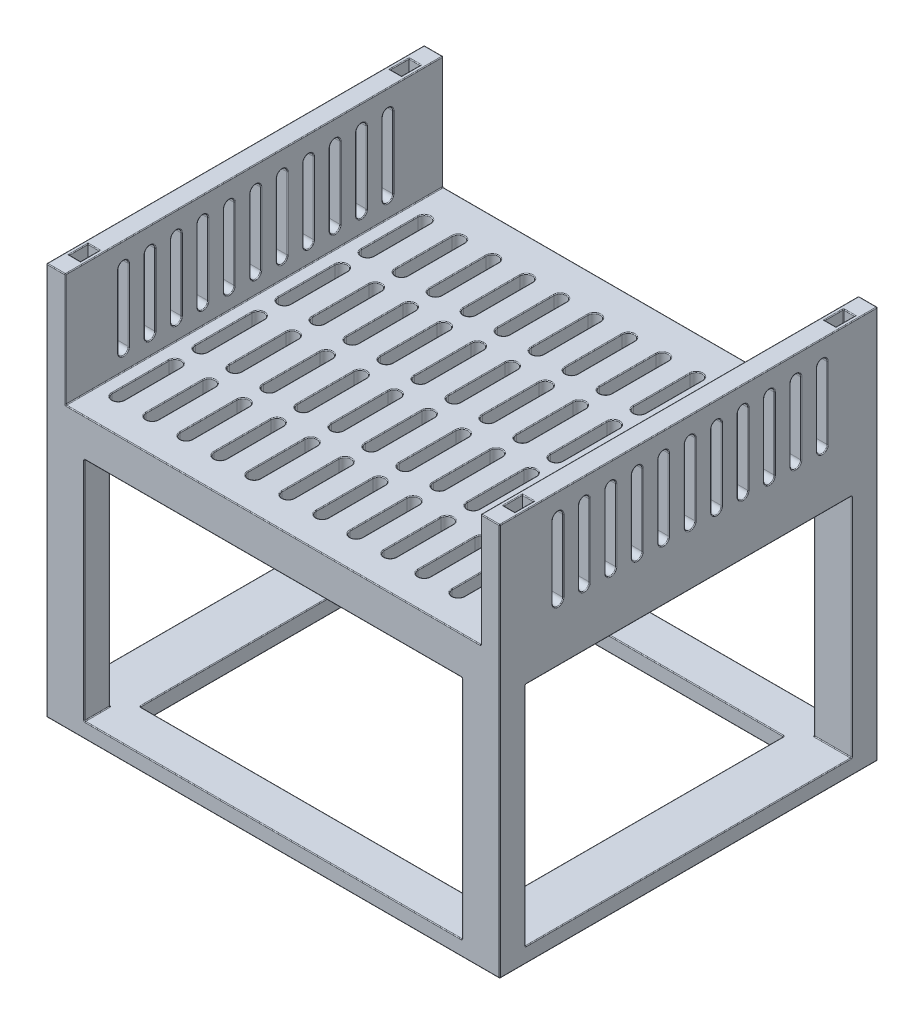
SolidWorks part; units mm, degrees
ref_plane "Plano frontal" through (0, 0, 0) normal (0, 0, 1) x (1, 0, 0)
ref_plane "Plano superior" through (0, 0, 0) normal (0, 1, 0) x (1, 0, 0)
ref_plane "Plano direito" through (0, 0, 0) normal (1, 0, 0) x (0, 0, -1)
sketch "Esboço1" plane through (0, 0, 0) normal (0, 1, 0) x (1, 0, 0)
  line L1 (0, 0) -> (600, 0)
  line L2 (0, 0) -> (0, 500)
  line L3 (0, 500) -> (600, 500)
  line L4 (600, 0) -> (600, 500)
  dimension "D1" = 500
  dimension "D2" = 600
extrude "Ressalto-extrusão1" add sketch "Esboço1" along normal blind 50
sketch "Esboço3" plane through (0, 50, 0) normal (0, 1, 0) x (1, 0, 0)
  line L0 (0, 0) -> (600, 0) construction
  line L1 (0, 500) -> (25, 500)
  line L2 (0, 500) -> (0, 0)
  line L3 (0, 0) -> (25, 0)
  line L4 (25, 500) -> (25, 0)
  line L6 (600, 500) -> (575, 500)
  line L7 (600, 500) -> (600, 0)
  line L8 (600, 0) -> (575, 0)
  line L9 (575, 500) -> (575, 0)
  dimension "D1" = 25
  dimension "D2" = 25
extrude "Ressalto-extrusão2" add sketch "Esboço3" along normal blind 150
sketch "Esboço13" plane through (0, 0, 0) normal (0, -1, 0) x (1, 0, 0)
  line L0 (50, -45) -> (50, -120) construction
  line L1 (58, -45) -> (58, -120)
  line L2 (42, -45) -> (42, -120)
  line L3 (0, -500) -> (0, 0) construction
  line L4 (0, 0) -> (600, 0) construction
  arc A0 (58, -45) -> (42, -45) centre (50, -45) ccw
  arc A1 (42, -120) -> (58, -120) centre (50, -120) ccw
  point P2 (50, -82.5)
  dimension "D2" = 8
  dimension "D1" = 75
  dimension "D3" = 50
  dimension "D4" = 45
extrude "Corte-extrusão6" cut sketch "Esboço13" against normal through all
pattern_linear "Padrão linear1" count 12 spacing 45 along (1, 0, 0) count 4 spacing 110 along (0, 0, -1) of "Corte-extrusão6"
sketch "Esboço15" plane through (0, 0, 0) normal (0, -1, 0) x (1, 0, 0)
  line L0 (300, 0) -> (300, -500) construction
  line L1 (0, 0) -> (50, 0)
  line L2 (0, 0) -> (0, -34)
  line L3 (0, -34) -> (50, -34)
  line L4 (50, 0) -> (50, -34)
  line L5 (0, 0) -> (600, 0) construction
  line L7 (0, -250) -> (600, -250) construction
  line L8 (0, -500) -> (0, 0) construction
  line L9 (600, 0) -> (600, -500) construction
  line L10 (550, 0) -> (550, -34)
  line L11 (600, -34) -> (550, -34)
  line L12 (600, 0) -> (600, -34)
  line L13 (600, 0) -> (550, 0)
  line L14 (600, -500) -> (550, -500)
  line L15 (600, -500) -> (600, -466)
  line L16 (600, -466) -> (550, -466)
  line L17 (550, -500) -> (550, -466)
  line L18 (50, -500) -> (50, -466)
  line L19 (0, -466) -> (50, -466)
  line L20 (0, -500) -> (0, -466)
  line L21 (0, -500) -> (50, -500)
  dimension "D1" = 34
  dimension "D2" = 50
extrude "Ressalto-extrusão4" add sketch "Esboço15" along normal blind 300
sketch "Esboço16" plane through (0, -300, 0) normal (0, -1, 0) x (1, 0, 0)
  line L0 (0, 0) -> (0, -34) construction
  line L1 (530, -54) -> (70, -54)
  line L2 (600, -54) -> (600, 0)
  line L3 (600, 0) -> (0, 0)
  line L4 (0, -51.6587) -> (0, 0)
  line L5 (50, 0) -> (0, 0) construction
  line L6 (600, -500) -> (600, -466) construction
  line L11 (50, -34) -> (50, 0) construction
  line L12 (0, 0) -> (70, 0)
  line L13 (0, 0) -> (0, -500)
  line L14 (0, -500) -> (70, -500)
  line L15 (70, -54) -> (70, -446)
  line L17 (50, -466) -> (0, -466) construction
  line L18 (0, -500) -> (600, -500)
  line L19 (0, -500) -> (0, -546)
  line L20 (70, -446) -> (530, -446)
  line L21 (600, -500) -> (600, -546)
  line L24 (600, 0) -> (530, 0)
  line L25 (600, 0) -> (600, -500)
  line L26 (600, -500) -> (530, -500)
  line L28 (550, -34) -> (600, -34) construction
  line L29 (530, -54) -> (530, -446)
  line L30 (550, 0) -> (550, -34) construction
  point P0 (300, -18.1706)
  line M18 (0, 0) -> (0, -34)
  line M19 (0, -34) -> (50, -34)
  line M20 (50, -34) -> (50, 0)
  line M21 (50, 0) -> (0, 0)
  dimension "D1" = 20
  dimension "D4" = 20
  dimension "D6" = 20
  dimension "D8" = 20
extrude "Ressalto-extrusão6" add sketch "Esboço16" along normal blind 20 contours L25 L2 L3 L4 L13 L14 L18 L21 L1 L29 L20 L15 M18 M21 M20 M19 | M21 M18 M19 M20
sketch "Esboço17" plane through (0, 200, 0) normal (0, 1, 0) x (1, 0, 0)
  line L0 (300, 500) -> (300, 0) construction
  line L1 (5, 475) -> (20, 475)
  line L2 (5, 475) -> (5, 450)
  line L3 (5, 450) -> (20, 450)
  line L4 (20, 475) -> (20, 450)
  line L5 (575, 500) -> (25, 500) construction
  line L6 (25, 0) -> (575, 0) construction
  line L7 (0, 250) -> (600, 250) construction
  line L8 (0, 500) -> (0, 0) construction
  line L9 (600, 0) -> (600, 500) construction
  line L10 (25, 500) -> (0, 500) construction
  line L12 (580, 475) -> (580, 450)
  line L13 (595, 450) -> (580, 450)
  line L14 (595, 475) -> (595, 450)
  line L15 (595, 475) -> (580, 475)
  line L16 (595, 25) -> (580, 25)
  line L17 (595, 25) -> (595, 50)
  line L18 (595, 50) -> (580, 50)
  line L19 (580, 25) -> (580, 50)
  line L20 (20, 25) -> (20, 50)
  line L21 (5, 50) -> (20, 50)
  line L22 (5, 25) -> (5, 50)
  line L23 (5, 25) -> (20, 25)
  dimension "D1" = 25
  dimension "D2" = 15
  dimension "D3" = 25
  dimension "D4" = 5
extrude "Corte-extrusão7" cut sketch "Esboço17" against normal blind 60
sketch "Esboço18" plane through (600, 0, 0) normal (1, 0, 0) x (0, 0, -1)
  line L0 (77, 170) -> (77, 75) construction
  line L1 (84, 170) -> (84, 75)
  line L2 (70, 170) -> (70, 75)
  line L3 (500, 50) -> (0, 50) construction
  arc A0 (84, 170) -> (70, 170) centre (77, 170) ccw
  arc A1 (70, 75) -> (84, 75) centre (77, 75) ccw
  point P2 (77, 122.5)
  point P7 (32, 127.9392)
  point P8 (69.0908, 142.4831)
  point P10 (69.6746, 124.6278)
  dimension "D1" = 7
  dimension "D2" = 95
  dimension "D3" = 25
  dimension "D4" = 20
extrude "Corte-extrusão8" cut sketch "Esboço18" against normal through all
pattern_linear "Padrão linear2" count 11 spacing 35 along (0, 0, -1) of "Corte-extrusão8"
fillet "Filete1" radius 1 649 edges at (320, 0, -37) (328, 0, -82.5) (320, 0, -128) (312, 0, -82.5) (320, 50, -37) (312, 50, -82.5) (320, 50, -128) (328, 50, -82.5) (365, 0, -37) (373, 0, -82.5) (365, 0, -128) (357, 0, -82.5) (365, 50, -37) (357, 50, -82.5) (365, 50, -128) (373, 50, -82.5) (410, 0, -37) (418, 0, -82.5) (410, 0, -128) (402, 0, -82.5) (410, 50, -37) (402, 50, -82.5) (410, 50, -128) (418, 50, -82.5) (455, 0, -37) (463, 0, -82.5) (455, 0, -128) (447, 0, -82.5) (455, 50, -37) (447, 50, -82.5) (455, 50, -128) (463, 50, -82.5) (500, 0, -37) (508, 0, -82.5) (300, 50, 0) (500, 0, -128) (492, 0, -82.5) (500, 50, -37) (492, 50, -82.5) (500, 50, -128) (508, 50, -82.5) (545, 0, -37) (553, 0, -82.5) (545, 0, -128) (537, 0, -82.5) (545, 50, -37) (537, 50, -82.5) (545, 50, -128) (553, 50, -82.5) (50, 0, -147) (58, 0, -192.5) (50, 0, -238) (42, 0, -192.5) (50, 50, -147) (42, 50, -192.5) (50, 50, -238) (58, 50, -192.5) (25, 50, -250) (25, 125, 0) (95, 0, -147) (103, 0, -192.5) (95, 0, -238) (87, 0, -192.5) (95, 50, -147) (87, 50, -192.5) (25, 125, -500) (95, 50, -238) (103, 50, -192.5) (0, 200, -250) (12.5, 200, 0) (140, 0, -147) (148, 0, -192.5) (140, 0, -238) (25, 200, -250) (132, 0, -192.5) (140, 50, -147) (132, 50, -192.5) (140, 50, -238) (148, 50, -192.5) (12.5, 200, -500) (185, 0, -147) (193, 0, -192.5) (185, 0, -238) (177, 0, -192.5) (185, 50, -147) (177, 50, -192.5) (185, 50, -238) (193, 50, -192.5) (230, 0, -147) (238, 0, -192.5) (230, 0, -238) (222, 0, -192.5) (230, 50, -147) (222, 50, -192.5) (230, 50, -238) (238, 50, -192.5) (275, 0, -147) (283, 0, -192.5) (275, 0, -238) (267, 0, -192.5) (275, 50, -147) (267, 50, -192.5) (275, 50, -238) (283, 50, -192.5) (320, 0, -147) (328, 0, -192.5) (320, 0, -238) (312, 0, -192.5) (320, 50, -147) (312, 50, -192.5) (320, 50, -238) (328, 50, -192.5) (365, 0, -147) (373, 0, -192.5) (365, 0, -238) (357, 0, -192.5) (365, 50, -147) (357, 50, -192.5) (365, 50, -238) (373, 50, -192.5) (410, 0, -147) (418, 0, -192.5) (410, 0, -238) (402, 0, -192.5) (410, 50, -147) (402, 50, -192.5) (410, 50, -238) (418, 50, -192.5) (455, 0, -147) (463, 0, -192.5) (455, 0, -238) (447, 0, -192.5) (455, 50, -147) (447, 50, -192.5) (455, 50, -238) (463, 50, -192.5) (500, 0, -147) (508, 0, -192.5) (500, 0, -238) (492, 0, -192.5) (500, 50, -147) (492, 50, -192.5) (500, 50, -238) (508, 50, -192.5) (545, 0, -147) (553, 0, -192.5) (545, 0, -238) (537, 0, -192.5) (545, 50, -147) (537, 50, -192.5) (545, 50, -238) (553, 50, -192.5) (300, 50, -500) (50, 0, -257) (58, 0, -302.5) (50, 0, -348) (42, 0, -302.5) (50, 50, -257) (42, 50, -302.5) (50, 50, -348) (58, 50, -302.5) (95, 0, -257) (103, 0, -302.5) (95, 0, -348) (87, 0, -302.5) (95, 50, -257) (87, 50, -302.5) (95, 50, -348) (103, 50, -302.5) (575, 50, -250) (140, 0, -257) (148, 0, -302.5) (140, 0, -348) (132, 0, -302.5) (575, 125, -500) (140, 50, -257) (132, 50, -302.5) (140, 50, -348) (148, 50, -302.5) (575, 125, 0) (600, 200, -250) (185, 0, -257) (193, 0, -302.5) (185, 0, -348) (177, 0, -302.5) (587.5, 200, -500) (185, 50, -257) (177, 50, -302.5) (185, 50, -348) (193, 50, -302.5) (575, 200, -250) (587.5, 200, 0) (230, 0, -257) (238, 0, -302.5) (230, 0, -348) (222, 0, -302.5) (230, 50, -257) (222, 50, -302.5) (230, 50, -348) (238, 50, -302.5) (275, 0, -257) (283, 0, -302.5) (275, 0, -348) (267, 0, -302.5) (275, 50, -257) (267, 50, -302.5) (275, 50, -348) (283, 50, -302.5) (320, 0, -257) (328, 0, -302.5) (320, 0, -348) (312, 0, -302.5) (320, 50, -257) (312, 50, -302.5) (320, 50, -348) (328, 50, -302.5) (365, 0, -257) (373, 0, -302.5) (365, 0, -348) (357, 0, -302.5) (365, 50, -257) (357, 50, -302.5) (365, 50, -348) (373, 50, -302.5) (410, 0, -257) (418, 0, -302.5) (410, 0, -348) (402, 0, -302.5) (410, 50, -257) (402, 50, -302.5) (410, 50, -348) (418, 50, -302.5) (455, 0, -257) (463, 0, -302.5) (455, 0, -348) (447, 0, -302.5) (455, 50, -257) (447, 50, -302.5) (455, 50, -348) (463, 50, -302.5) (500, 0, -257) (508, 0, -302.5) (500, 0, -348) (492, 0, -302.5) (500, 50, -257) (492, 50, -302.5) (500, 50, -348) (508, 50, -302.5) (545, 0, -257) (553, 0, -302.5) (545, 0, -348) (537, 0, -302.5) (545, 50, -257) (537, 50, -302.5) (545, 50, -348) (553, 50, -302.5) (50, 0, -367) (58, 0, -412.5) (50, 0, -458) (42, 0, -412.5) (50, 50, -367) (42, 50, -412.5) (50, 50, -458) (58, 50, -412.5) (95, 0, -367) (103, 0, -412.5) (95, 0, -458) (87, 0, -412.5) (95, 50, -367) (87, 50, -412.5) (95, 50, -458) (103, 50, -412.5) (140, 0, -367) (148, 0, -412.5) (140, 0, -458) (132, 0, -412.5) (140, 50, -367) (132, 50, -412.5) (140, 50, -458) (148, 50, -412.5) (185, 0, -367) (193, 0, -412.5) (185, 0, -458) (177, 0, -412.5) (185, 50, -367) (177, 50, -412.5) (185, 50, -458) (193, 50, -412.5) (230, 0, -367) (238, 0, -412.5) (230, 0, -458) (222, 0, -412.5) (230, 50, -367) (222, 50, -412.5) (230, 50, -458) (238, 50, -412.5) (275, 0, -367) (283, 0, -412.5) (275, 0, -458) (267, 0, -412.5) (275, 50, -367) (267, 50, -412.5) (275, 50, -458) (283, 50, -412.5) (320, 0, -367) (328, 0, -412.5) (320, 0, -458) (312, 0, -412.5) (320, 50, -367) (312, 50, -412.5) (320, 50, -458) (328, 50, -412.5) (365, 0, -367) (373, 0, -412.5) (365, 0, -458) (357, 0, -412.5) (365, 50, -367) (357, 50, -412.5) (365, 50, -458) (373, 50, -412.5) (410, 0, -367) (418, 0, -412.5) (410, 0, -458) (402, 0, -412.5) (410, 50, -367) (402, 50, -412.5) (410, 50, -458) (418, 50, -412.5) (50, 50, -37) (58, 50, -82.5) (455, 0, -367) (463, 0, -412.5) (455, 0, -458) (447, 0, -412.5) (455, 50, -367) (447, 50, -412.5) (455, 50, -458) (50, 50, -128) (463, 50, -412.5) (42, 50, -82.5) (500, 0, -367) (508, 0, -412.5) (500, 0, -458) (492, 0, -412.5) (500, 50, -367) (492, 50, -412.5) (500, 50, -458) (508, 50, -412.5) (545, 0, -367) (553, 0, -412.5) (545, 0, -458) (537, 0, -412.5) (545, 50, -367) (537, 50, -412.5) (545, 50, -458) (553, 50, -412.5) (50, 0, -37) (42, 0, -82.5) (50, 0, -128) (58, 0, -82.5) (300, 0, 0) (25, 0, -34) (0, -150, -34) (50, 0, -17) (50, -150, -34) (50, -150, 0) (25, -300, -34) (50, -300, -17) (600, 0, -250) (550, 0, -17) (550, -150, 0) (575, 0, -34) (550, -150, -34) (600, -150, -34) (550, -300, -17) (575, -300, -34) (300, 0, -500) (575, 0, -466) (600, -150, -466) (550, 0, -483) (550, -150, -466) (550, -150, -500) (575, -300, -466) (550, -300, -483) (0, 0, -250) (50, 0, -483) (50, -150, -500) (25, 0, -466) (50, -150, -466) (0, -150, -466) (50, -300, -483) (25, -300, -466) (300, -300, -54) (70, -300, -250) (300, -300, -446) (0, -300, -250) (600, -300, -250) (300, -320, -54) (70, -310, -54) (530, -300, -250) (530, -310, -54) (300, -320, -446) (530, -310, -446) (300, -300, 0) (0, -320, -250) (300, -300, -500) (600, -320, -250) (70, -320, -250) (70, -310, -446) (300, -320, 0) (300, -320, -500) (530, -320, -250) (95, 0, -37) (12.5, 200, -25) (20, 200, -37.5) (87, 0, -82.5) (12.5, 200, -50) (5, 200, -37.5) (95, 0, -128) (103, 0, -82.5) (580, 170, -475) (587.5, 200, -475) (580, 200, -462.5) (95, 50, -37) (587.5, 200, -450) (595, 200, -462.5) (103, 50, -82.5) (595, 200, -37.5) (587.5, 200, -50) (580, 200, -37.5) (95, 50, -128) (587.5, 200, -25) (87, 50, -82.5) (5, 200, -462.5) (12.5, 200, -450) (20, 200, -462.5) (12.5, 200, -475) (575, 122.5, -70) (575, 68, -77) (575, 122.5, -84) (575, 177, -77) (25, 177, -77) (0, 177, -77) (25, 122.5, -84) (0, 122.5, -84) (25, 68, -77) (0, 68, -77) (25, 122.5, -70) (0, 122.5, -70) (600, 177, -77) (600, 122.5, -70) (600, 68, -77) (600, 122.5, -84) (140, 0, -37) (148, 0, -82.5) (140, 0, -128) (132, 0, -82.5) (25, 177, -112) (0, 177, -112) (25, 122.5, -119) (0, 122.5, -119) (25, 68, -112) (0, 68, -112) (25, 122.5, -105) (0, 122.5, -105) (140, 50, -37) (132, 50, -82.5) (140, 50, -128) (0, 177, -147) (0, 122.5, -140) (0, 68, -147) (0, 122.5, -154) (25, 177, -147) (25, 122.5, -154) (25, 68, -147) (25, 122.5, -140) (148, 50, -82.5) (0, 177, -182) (0, 122.5, -175) (0, 68, -182) (0, 122.5, -189) (25, 177, -182) (25, 122.5, -189) (25, 68, -182) (25, 122.5, -175) (0, 177, -217) (0, 122.5, -210) (0, 68, -217) (0, 122.5, -224) (25, 177, -217) (25, 122.5, -224) (25, 68, -217) (25, 122.5, -210) (0, 177, -252) (0, 122.5, -245) (0, 68, -252) (0, 122.5, -259) (25, 177, -252) (25, 122.5, -259) (25, 68, -252) (25, 122.5, -245) (0, -60, -500) (0, 177, -287) (0, 122.5, -280) (0, 68, -287) (0, 122.5, -294) (25, 177, -287) (25, 122.5, -294) (25, 68, -287) (25, 122.5, -280) (600, -60, -500) (0, 177, -322) (0, 122.5, -315) (0, 68, -322) (0, 122.5, -329) (25, 177, -322) (25, 122.5, -329) (25, 68, -322) (25, 122.5, -315) (0, 177, -357) (0, 122.5, -350) (0, 68, -357) (0, 122.5, -364) (25, 177, -357) (600, -60, 0) (25, 122.5, -364) (25, 68, -357) (25, 122.5, -350) (0, 177, -392) (0, 122.5, -385) (0, 68, -392) (0, 122.5, -399) (25, 177, -392) (25, 122.5, -399) (25, 68, -392) (25, 122.5, -385) (0, -60, 0) (185, 0, -37) (0, 177, -427) (0, 122.5, -420) (193, 0, -82.5) (0, 68, -427) (0, 122.5, -434) (25, 177, -427) (25, 122.5, -434) (25, 68, -427) (25, 122.5, -420) (185, 0, -128) (177, 0, -82.5) (185, 50, -37) (177, 50, -82.5) (185, 50, -128) (193, 50, -82.5) (600, 122.5, -105) (600, 68, -112) (600, 122.5, -119) (600, 177, -112) (575, 122.5, -105) (575, 68, -112) (575, 122.5, -119) (575, 177, -112) (600, 122.5, -140) (600, 177, -147) (600, 122.5, -154) (600, 68, -147) (575, 122.5, -140) (575, 68, -147) (575, 122.5, -154) (575, 177, -147) (600, 122.5, -175) (600, 177, -182) (600, 122.5, -189) (600, 68, -182) (575, 122.5, -175) (575, 68, -182) (575, 122.5, -189) (575, 177, -182) (600, 122.5, -210) (600, 177, -217) (600, 122.5, -224) (600, 68, -217) (575, 122.5, -210) (575, 68, -217) (575, 122.5, -224) (575, 177, -217) (600, 122.5, -245) (600, 177, -252) (600, 122.5, -259) (600, 68, -252) (575, 122.5, -245) (575, 68, -252) (575, 122.5, -259) (575, 177, -252) (600, 122.5, -280) (600, 177, -287) (600, 122.5, -294) (600, 68, -287) (575, 122.5, -280) (575, 68, -287) (575, 122.5, -294) (575, 177, -287) (600, 122.5, -315) (600, 177, -322) (600, 122.5, -329) (600, 68, -322) (575, 122.5, -315) (575, 68, -322) (575, 122.5, -329) (575, 177, -322) (600, 122.5, -350) (600, 177, -357) (600, 122.5, -364) (230, 0, -37) (600, 68, -357) (575, 122.5, -350) (575, 68, -357) (575, 122.5, -364) (575, 177, -357) (238, 0, -82.5) (230, 0, -128) (600, 122.5, -385) (600, 177, -392) (600, 122.5, -399) (600, 68, -392) (575, 122.5, -385) (575, 68, -392) (575, 122.5, -399) (222, 0, -82.5) (575, 177, -392) (230, 50, -37) (222, 50, -82.5) (600, 122.5, -420) (600, 177, -427) (600, 122.5, -434) (600, 68, -427) (575, 122.5, -420) (575, 68, -427) (575, 122.5, -434) (575, 177, -427) (230, 50, -128) (238, 50, -82.5) (275, 0, -37) (283, 0, -82.5) (275, 0, -128) (267, 0, -82.5) (275, 50, -37) (267, 50, -82.5) (275, 50, -128) (283, 50, -82.5)
